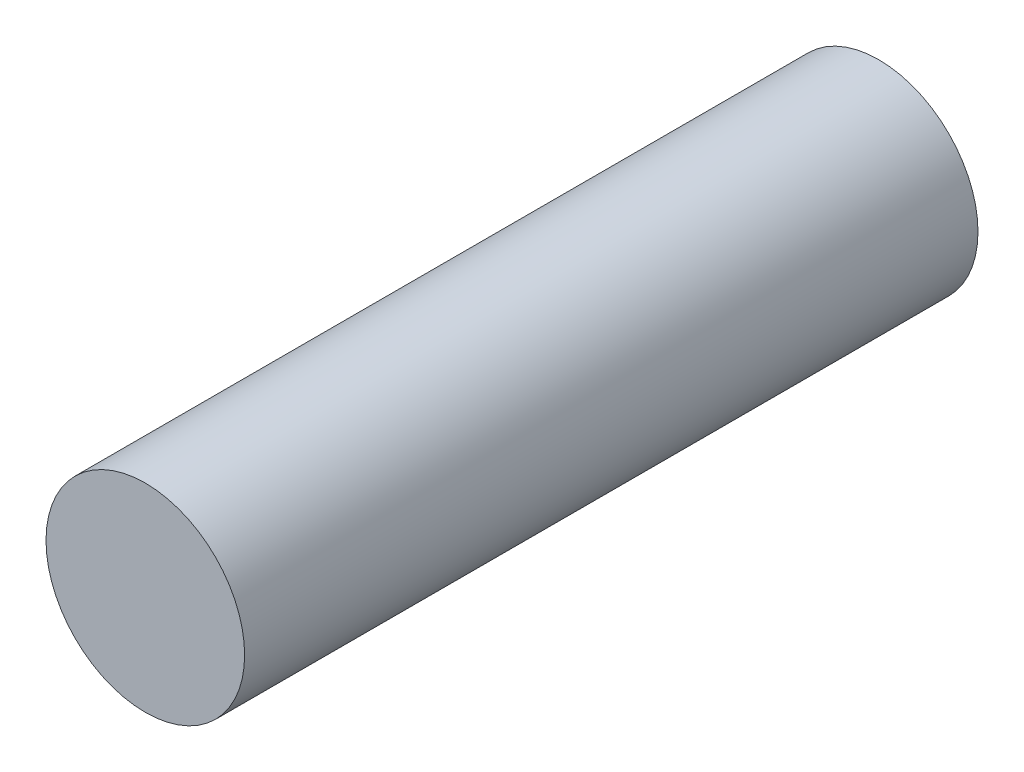
SolidWorks part; units mm, degrees
material "Plain Carbon Steel"
ref_plane "Front Plane" through (0, 0, 0) normal (0, 0, 1) x (1, 0, 0)
ref_plane "Top Plane" through (0, 0, 0) normal (0, 1, 0) x (1, 0, 0)
ref_plane "Right Plane" through (0, 0, 0) normal (1, 0, 0) x (0, 0, -1)
sketch "Sketch1" plane through (0, 0, 0) normal (0, 0, 1) x (1, 0, 0)
  circle A0 centre (0, 0) radius 6.5
  dimension "D1" = 13
extrude "Boss-Extrude1" add sketch "Sketch1" along normal mid plane 48
